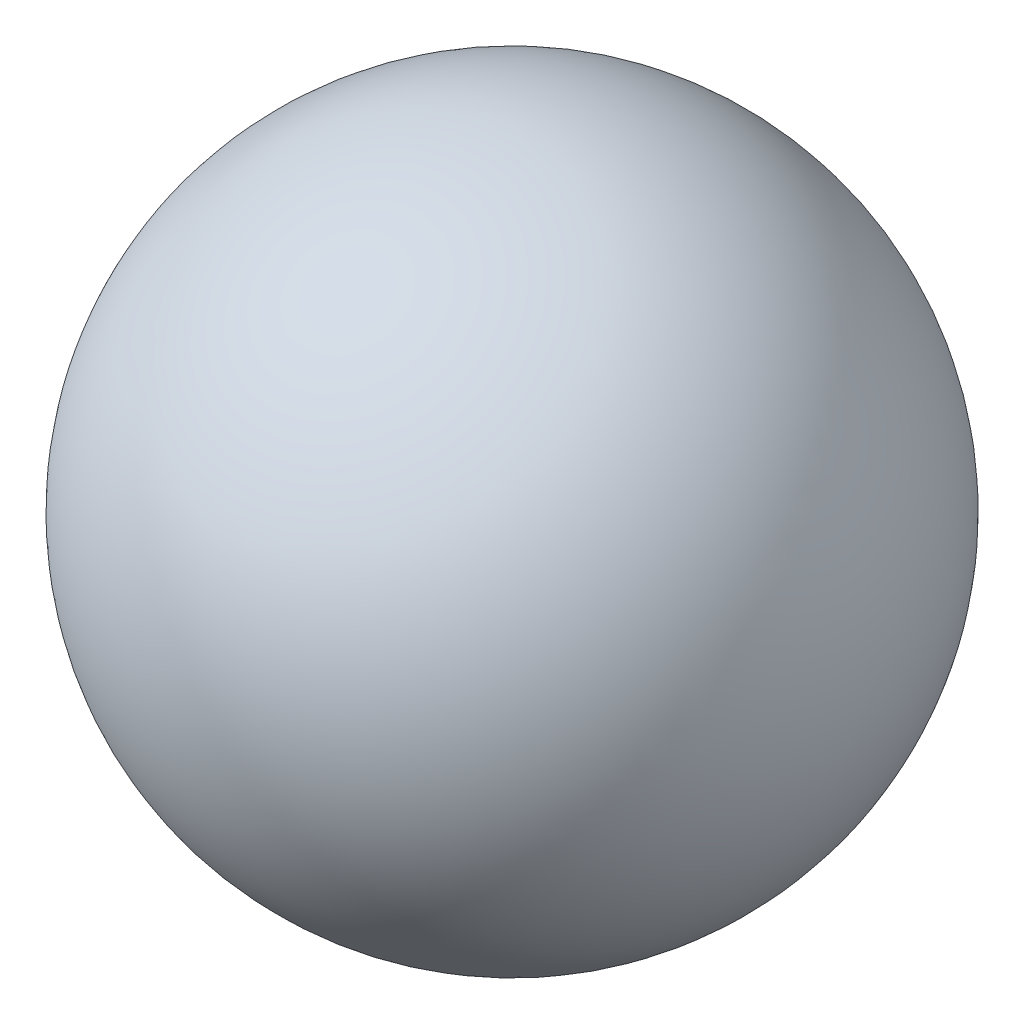
SolidWorks part; units mm, degrees
ref_plane "Plan1" through (0, 0, 0) normal (0, 0, 1) x (1, 0, 0)
ref_plane "Plan2" through (0, 0, 0) normal (0, 1, 0) x (1, 0, 0)
ref_plane "Plan3" through (0, 0, 0) normal (1, 0, 0) x (0, 0, -1)
sketch "Esquisse1" plane through (0, 0, 0) normal (0, 1, 0) x (1, 0, 0)
  line L1 (-0.3, 3.95) -> (8.7, 3.95) construction
  line L2 (-0.3, 7.9) -> (-0.3, 0) construction
  line L3 (8.7, 7.9) -> (8.7, 0) construction
  line L4 (1.65, 3.95) -> (6.75, 3.95)
  circle A1 centre (4.2, 3.95) radius 2.55 construction
  arc A2 (6.75, 3.95) -> (1.65, 3.95) centre (4.2, 3.95) ccw
revolve "Base-Révolution" add sketch "Esquisse1" angle 360 about L1
